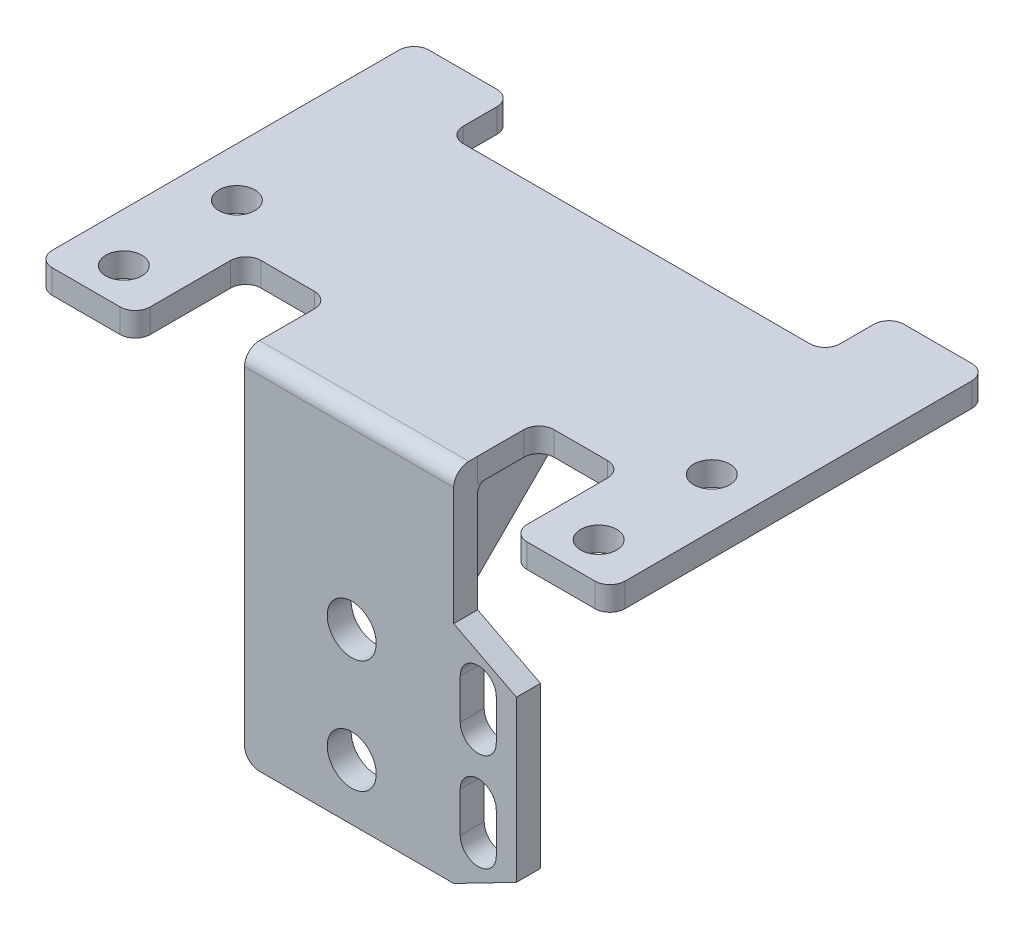
SolidWorks part; units mm, degrees
ref_plane "Front" through (0, 0, 0) normal (0, 0, 1) x (1, 0, 0)
ref_plane "Top" through (0, 0, 0) normal (0, 1, 0) x (1, 0, 0)
ref_plane "Right" through (0, 0, 0) normal (1, 0, 0) x (0, 0, -1)
sketch "Sketch1" plane through (0, 0, 0) normal (0, 1, 0) x (1, 0, 0)
  line L0 (0, 0) -> (0, 50)
  line L1 (0, 50) -> (13, 50)
  line L2 (13, 50) -> (13, 41.5219)
  line L3 (13, 41.5219) -> (63, 41.5219)
  line L4 (63, 41.5219) -> (63, 50)
  line L5 (63, 50) -> (76, 50)
  line L6 (76, 50) -> (76, 0)
  line L7 (76, 0) -> (63, 0)
  line L8 (63, 0) -> (63, 14.6853)
  line L9 (63, 14.6853) -> (51.88, 14.6853)
  line L10 (13, 14.6853) -> (13, 0)
  line L11 (13, 0) -> (0, 0)
  line L12 (24.12, 14.6853) -> (24.12, 6.5669)
  line L13 (24.12, 6.5669) -> (51.88, 6.5669)
  line L14 (51.88, 6.5669) -> (51.88, 14.6853)
  line L16 (24.12, 14.6853) -> (13, 14.6853)
  dimension "D1" = 76
  dimension "D2" = 13
  dimension "D3" = 13
  dimension "D4" = 27.76
  dimension "D5" = 50
  dimension "D6" = 8.4781
extrude "Boss-Extrude2" add sketch "Sketch1" against normal blind 3.18
sketch "Sketch8" plane through (0, 0, -6.5669) normal (0, 0, 1) x (1, 0, 0)
  line L0 (24.12, -45.5) -> (24.12, -20.1534)
  line L2 (51.8796, -17.65) -> (60.2044, -21.94)
  line L3 (60.2044, -21.94) -> (60.2044, -43.21)
  line L4 (60.2044, -43.21) -> (51.8796, -47.5)
  line L8 (51.8796, -47.5) -> (26.12, -47.5)
  line L12 (51.8796, 0) -> (51.8796, -17.65)
  line L13 (24.12, -20.1534) -> (24.12, 0)
  line L14 (24.12, 0) -> (51.8796, 0)
  line L15 (55.1344, -23.2235) -> (55.1344, -28.5469) construction
  line L16 (57.5244, -23.2235) -> (57.5244, -28.5469)
  line L17 (52.7444, -23.2235) -> (52.7444, -28.5469)
  line L18 (55.1344, -36.2235) -> (55.1344, -41.5469) construction
  line L19 (57.5244, -36.2235) -> (57.5244, -41.5469)
  line L20 (52.7444, -36.2235) -> (52.7444, -41.5469)
  line L27 (13, -3.18) -> (13, 0) construction
  circle A0 centre (38.3488, -25.08) radius 3.25
  circle A1 centre (38.3488, -40.08) radius 3.25
  arc A3 (57.5244, -23.2235) -> (52.7444, -23.2235) centre (55.1344, -23.2235) ccw
  arc A4 (52.7444, -28.5469) -> (57.5244, -28.5469) centre (55.1344, -28.5469) ccw
  arc A5 (57.5244, -36.2235) -> (52.7444, -36.2235) centre (55.1344, -36.2235) ccw
  arc A6 (52.7444, -41.5469) -> (57.5244, -41.5469) centre (55.1344, -41.5469) ccw
  arc A7 (26.12, -47.5) -> (24.12, -45.5) centre (26.12, -45.5) cw
  point P19 (55.1344, -25.8852)
  point P24 (55.1344, -38.8852)
  dimension "D7" = 2
  dimension "D1" = 47.5
  dimension "D2" = 21.27
  dimension "D3" = 29.85
  dimension "D4" = 2.68
  dimension "D5" = 15
  dimension "D6" = 7.42
  dimension "D8" = 11.12
  dimension "D9" = 27.7596
extrude "Boss-Extrude3" add sketch "Sketch8" along normal blind 3.18
fillet "Fillet4" radius 2 1 edges at (37.9998, 0, -3.3869)
fillet "Fillet5" radius 1 1 edges at (37.9998, -3.18, -6.5669)
sketch "Sketch9" plane through (0, 0, 0) normal (0, 1, 0) x (1, 0, 0)
  line L1 (0, 50) -> (0, 0) construction
  line L2 (0, 0) -> (13, 0) construction
  circle A0 centre (6.5, 5) radius 2.39
  circle A1 centre (6.5, 20) radius 2.39
  circle A2 centre (69.5, 20) radius 2.39
  circle A3 centre (69.5, 5) radius 2.39
  dimension "D1" = 4.78
  dimension "D2" = 15
  dimension "D3" = 6.5
  dimension "D4" = 6.5
  dimension "D5" = 5
extrude "Cut-Extrude1" cut sketch "Sketch9" against normal blind 3.18
fillet "Fillet6" radius 2 1 edges at (0, -1.59, 0)
fillet "Fillet7" radius 2 1 edges at (13, -1.59, 0)
fillet "Fillet8" radius 2 12 edges at (51.88, -1.59, -14.6853) (13, -1.59, -14.6853) (13, -1.59, -41.5219) (63, -1.59, -41.5219) (76, -1.59, -50) (63, -1.59, -50) (0, -1.59, -50) (13, -1.59, -50) (63, -1.59, -14.6853) (24.12, -1.59, -14.6853) (76, -1.59, 0) (63, -1.59, 0)
sketch "Sketch4" [suppressed] plane through (0, 0, 0) normal (0, 0, 1) x (1, 0, 0)
  line L0 (-14.0978, 0) -> (-14.0978, 45)
  line L1 (-11.5978, 47.5) -> (13.6618, 47.5)
  line L2 (13.6618, 47.5) -> (21.2228, 43.2094)
  line L3 (21.2228, 43.2094) -> (21.2228, 21.944)
  line L4 (21.2228, 21.944) -> (13.6618, 17.6534)
  line L5 (13.6618, 17.6534) -> (13.6618, 3.18)
  line L6 (13.6618, 3.18) -> (13.6618, 0)
  line L7 (13.6618, 0) -> (-14.0978, 0)
  arc A0 (-11.5978, 47.5) -> (-14.0978, 45) centre (-11.5978, 45) ccw
  dimension "D1" = 2.5
  dimension "D2" = 45
sketch "Sketch3" [suppressed] plane through (0, 0, 0) normal (0, 0, 1) x (1, 0, 0)
  circle A0 centre (-0.2978, 40.0831) radius 3.25
  circle A1 centre (-0.2978, 25.0831) radius 3.25
  dimension "D1" = 6.5
  dimension "D2" = 6.5
  dimension "D3" = 15
sketch "Sketch5" [suppressed] plane through (0, 0, 0) normal (0, 0, 1) x (1, 0, 0)
  line L0 (16.1496, 41.3556) -> (16.1496, 36.0322) construction
  line L1 (18.5396, 41.3556) -> (18.5396, 36.0322)
  line L2 (13.7596, 41.3556) -> (13.7596, 36.0322)
  line L3 (16.1496, 28.3556) -> (16.1496, 23.0322) construction
  line L4 (18.5396, 28.3556) -> (18.5396, 23.0322)
  line L5 (13.7596, 28.3556) -> (13.7596, 23.0322)
  arc A0 (18.5396, 41.3556) -> (13.7596, 41.3556) centre (16.1496, 41.3556) ccw
  arc A1 (13.7596, 36.0322) -> (18.5396, 36.0322) centre (16.1496, 36.0322) ccw
  arc A2 (18.5396, 28.3556) -> (13.7596, 28.3556) centre (16.1496, 28.3556) ccw
  arc A3 (13.7596, 23.0322) -> (18.5396, 23.0322) centre (16.1496, 23.0322) ccw
  point P2 (16.1496, 38.6939)
  point P7 (16.1496, 25.6939)
  dimension "D1" = 4.78
  dimension "D2" = 4.78
  dimension "D3" = 13
ref_plane "Plane3" through (38, 0, 0) normal (1, 0, 0) x (0, 0, -1)
sketch "Sketch11" plane through (38, 0, 0) normal (1, 0, 0) x (0, 0, -1)
  line L0 (25, -3.18) -> (6.5454, -3.18)
  line L1 (2, -3.18) -> (48, -3.18) construction
  line L2 (6.5454, -3.18) -> (6.5454, -21.6346)
  line L3 (6.5454, -21.6346) -> (25, -3.18)
  point P6 (10, -18.18)
  dimension "D2" = 45
extrude "Boss-Extrude6" add sketch "Sketch11" along normal mid plane 20
sketch "Sketch12" plane through (0, 0, -6.5669) normal (0, 0, -1) x (-1, 0, 0)
  circle A0 centre (-38.3488, -25.08) radius 7.8945
extrude "Cut-Extrude2" cut sketch "Sketch12" along normal blind 20
